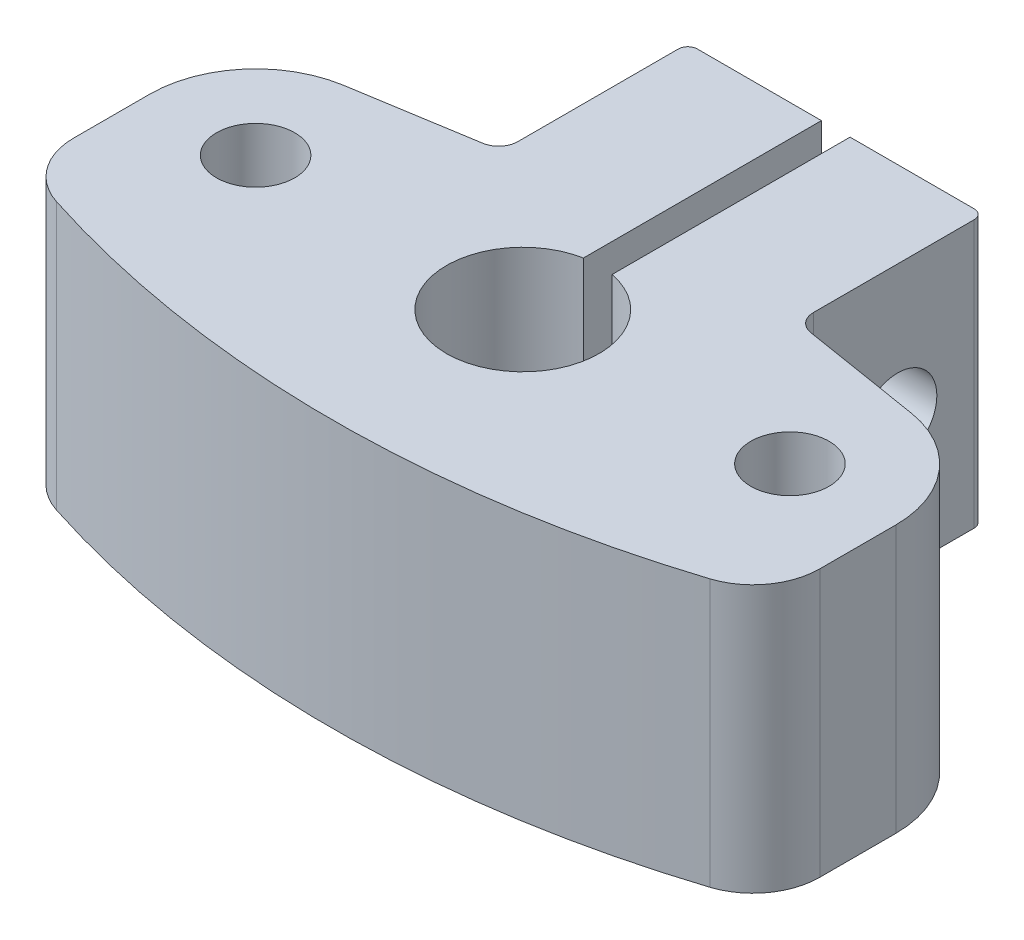
SolidWorks part; units mm, degrees
ref_plane "Front Plane" through (0, 0, 0) normal (0, 0, 1) x (1, 0, 0)
ref_plane "Top Plane" through (0, 0, 0) normal (0, 1, 0) x (1, 0, 0)
ref_plane "Right Plane" through (0, 0, 0) normal (1, 0, 0) x (0, 0, -1)
sketch "Sketch1" plane through (0, 0, 0) normal (0, 1, 0) x (1, 0, 0)
  line L0 (-19.55, 0) -> (-19.55, -3.9865)
  line L1 (19.55, 0) -> (19.55, -3.9865)
  line L2 (0, 0) -> (0, 16.4) construction
  line L3 (0.75, 3.9291) -> (0.75, 16.4)
  line L4 (-0.75, 3.9291) -> (-0.75, 16.4)
  line L5 (-7.25, 16.4) -> (-0.75, 16.4)
  line L6 (7.75, 7.4871) -> (7.75, 15.9)
  line L7 (-7.75, 7.4871) -> (-7.75, 15.9)
  line L8 (7.75, 0) -> (7.75, 16.6498) construction
  line L9 (-7.75, 0) -> (-7.75, 16.6498) construction
  line L10 (-14.8886, 5.4784) -> (-8.5899, 6.5)
  line L11 (14.8886, 5.4784) -> (8.5899, 6.5)
  line L12 (0, 0) -> (0, 16.6498) construction
  line L13 (-0.75, 0) -> (-0.75, 16.6498) construction
  line L14 (0.75, 0) -> (0.75, 16.6498) construction
  line L15 (0.75, 16.4) -> (7.25, 16.4)
  arc A0 (-0.75, 3.9291) -> (0.75, 3.9291) centre (0, 0) ccw
  circle A1 centre (-14, 0) radius 2.05
  circle A2 centre (14, 0) radius 2.05
  arc A3 (-14.8886, 5.4784) -> (-19.55, 0) centre (-14, 0) ccw
  arc A4 (19.55, 0) -> (14.8886, 5.4784) centre (14, 0) ccw
  arc A5 (-17.12, -7.3189) -> (17.12, -7.3189) centre (0, 46) ccw
  arc A6 (7.75, 7.4871) -> (8.5899, 6.5) centre (8.75, 7.4871) ccw
  arc A7 (-7.75, 7.4871) -> (-8.5899, 6.5) centre (-8.75, 7.4871) cw
  arc A8 (7.75, 15.9) -> (7.25, 16.4) centre (7.25, 15.9) ccw
  arc A9 (-7.25, 16.4) -> (-7.75, 15.9) centre (-7.25, 15.9) ccw
  arc A10 (19.55, -3.9865) -> (17.12, -7.3189) centre (16.05, -3.9865) cw
  arc A11 (-19.55, -3.9865) -> (-17.12, -7.3189) centre (-16.05, -3.9865) ccw
  circle A12 centre (-14, 0) radius 5.55 construction
  circle A13 centre (14, 0) radius 5.55 construction
  dimension "D1" = 4.1
  dimension "D2" = 4.1
  dimension "D3" = 8
  dimension "D7" = 112
  dimension "D14" = 1
  dimension "D16" = 0.5
  dimension "D18" = 3.5
  dimension "D4" = 14
  dimension "D5" = 14
  dimension "D8" = 46
  dimension "D11" = 16.4
  dimension "D15" = 6.5
  dimension "D17" = 6.5
  dimension "D6" = 3.5
  dimension "D9" = 0.75
  dimension "D10" = 0.75
  dimension "D12" = 7
  dimension "D13" = 7
extrude "Boss-Extrude1" add sketch "Sketch1" along normal blind 14
sketch "Sketch2" plane through (7.75, 0, 0) normal (1, 0, 0) x (0, 0, -1)
  line L0 (16.4, 14) -> (16.4, 0) construction
  line L1 (7.4871, 14) -> (15.9, 14) construction
  circle A0 centre (11.9, 7) radius 2.05
  dimension "D1" = 4.5
  dimension "D3" = 4.1
  dimension "D2" = 7
extrude "Cut-Extrude1" cut sketch "Sketch2" against normal through all
